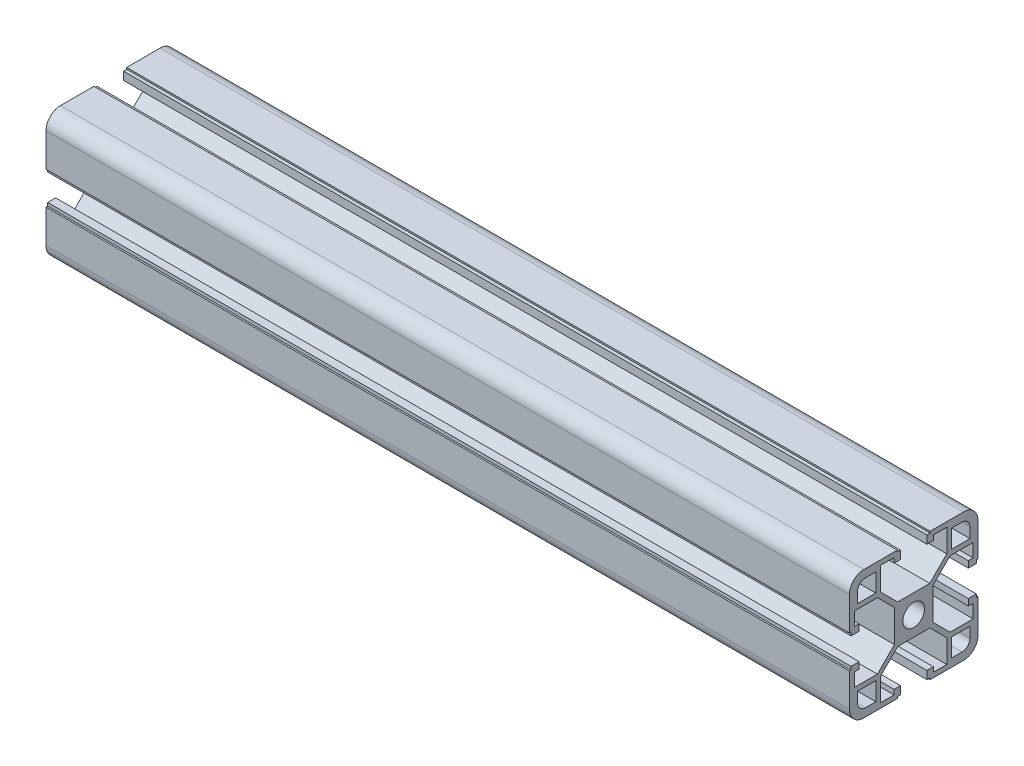
SolidWorks part; units mm, degrees
ref_plane "前视基准面" through (0, 0, 0) normal (0, 0, 1) x (1, 0, 0)
ref_plane "上视基准面" through (0, 0, 0) normal (0, 1, 0) x (1, 0, 0)
ref_plane "右视基准面" through (0, 0, 0) normal (1, 0, 0) x (0, 0, -1)
sketch "草图1" plane through (0, 0, 0) normal (0, 1, 0) x (1, 0, 0)
  line L0 (-142.4125, 0) -> (107.5875, 0)
  dimension "D1" = 250
other "铝型材 40 X 40L X R4.5(1)"
ref_plane "基准面1" through (-142.4125, 0, 0) normal (1, 0, 0) x (0, 0, -1)
sketch "Sketch1" plane through (-142.4125, 0, 0) normal (1, 0, 0) x (0, 0, -1)
  line L0 (-5.1, 20) -> (-5.1, 19.5)
  line L1 (-5.1, 19.5) -> (-4.1, 19.5)
  line L2 (-4.1, 19.5) -> (-4.1, 17)
  line L3 (-6.1, 18.5) -> (-10.3, 18.5)
  line L4 (-15.5, -20) -> (-5.1, -20)
  line L5 (-20, -15.5) -> (-20, -5.1)
  line L6 (15.5, 20) -> (5.1, 20)
  line L7 (20, 15.5) -> (20, 5.1)
  line L8 (0, 14.8756) -> (0, 0) construction
  line L9 (0, 0) -> (14.1675, 0) construction
  line L10 (-10.3, 18.5) -> (-10.3, 11.3)
  line L11 (-10.3, 11.3) -> (-5, 6)
  line L12 (-5, 6) -> (5, 6)
  line L13 (10.3, 11.3) -> (5, 6)
  line L14 (10.3, 18.5) -> (10.3, 11.3)
  line L15 (6.1, 18.5) -> (10.3, 18.5)
  line L16 (4.1, 19.5) -> (4.1, 17)
  line L17 (5.1, 19.5) -> (4.1, 19.5)
  line L18 (5.1, 20) -> (5.1, 19.5)
  line L19 (-5.1, 20) -> (-15.5, 20)
  line L20 (20, 5.1) -> (19.5, 5.1)
  line L21 (11.8, 17.5) -> (15, 17.5)
  line L22 (11.8, 17.5) -> (11.8, 11.8)
  line L23 (11.8, 11.8) -> (17.5, 11.8)
  line L24 (17.5, 15) -> (17.5, 11.8)
  line L25 (19.5, 5.1) -> (19.5, 4.1)
  line L26 (19.5, 4.1) -> (17, 4.1)
  line L27 (17, 6.1) -> (17, 4.1)
  line L28 (18.5, 6.1) -> (17, 6.1)
  line L29 (18.5, 6.1) -> (18.5, 10.3)
  line L30 (18.5, 10.3) -> (11.3, 10.3)
  line L31 (11.3, 10.3) -> (6, 5)
  line L32 (6, 5) -> (6, -5)
  line L33 (11.3, -10.3) -> (6, -5)
  line L34 (18.5, -10.3) -> (11.3, -10.3)
  line L35 (18.5, -6.1) -> (18.5, -10.3)
  line L36 (18.5, -6.1) -> (17, -6.1)
  line L37 (17, -4.1) -> (17, -6.1)
  line L38 (19.5, -4.1) -> (17, -4.1)
  line L39 (19.5, -5.1) -> (19.5, -4.1)
  line L40 (20, -5.1) -> (19.5, -5.1)
  line L41 (5.1, -20) -> (5.1, -19.5)
  line L42 (5.1, -19.5) -> (4.1, -19.5)
  line L43 (4.1, -19.5) -> (4.1, -17)
  line L44 (6.1, -17) -> (4.1, -17)
  line L45 (6.1, -18.5) -> (6.1, -17)
  line L46 (6.1, -18.5) -> (10.3, -18.5)
  line L47 (10.3, -18.5) -> (10.3, -11.3)
  line L48 (10.3, -11.3) -> (5, -6)
  line L49 (5, -6) -> (-5, -6)
  line L50 (-10.3, -11.3) -> (-5, -6)
  line L51 (-10.3, -18.5) -> (-10.3, -11.3)
  line L52 (-6.1, -18.5) -> (-10.3, -18.5)
  line L53 (-6.1, -18.5) -> (-6.1, -17)
  line L54 (-4.1, -17) -> (-6.1, -17)
  line L55 (-4.1, -19.5) -> (-4.1, -17)
  line L56 (-5.1, -19.5) -> (-4.1, -19.5)
  line L57 (-5.1, -20) -> (-5.1, -19.5)
  line L58 (-20, -5.1) -> (-19.5, -5.1)
  line L59 (5.1, -20) -> (15.5, -20)
  line L60 (-20, 5.1) -> (-20, 15.5)
  line L61 (-19.5, -5.1) -> (-19.5, -4.1)
  line L62 (-6.1, 18.5) -> (-6.1, 17)
  line L63 (-6.1, 17) -> (-4.1, 17)
  line L64 (6.1, 18.5) -> (6.1, 17)
  line L65 (4.1, 17) -> (6.1, 17)
  line L66 (-19.5, -4.1) -> (-17, -4.1)
  line L67 (-15, 17.5) -> (-11.8, 17.5)
  line L68 (-17.5, 15) -> (-17.5, 11.8)
  line L69 (-17.5, 11.8) -> (-11.8, 11.8)
  line L70 (-11.8, 17.5) -> (-11.8, 11.8)
  line L71 (-17, -6.1) -> (-17, -4.1)
  line L72 (-18.5, -6.1) -> (-17, -6.1)
  line L73 (-18.5, -6.1) -> (-18.5, -10.3)
  line L74 (-18.5, -10.3) -> (-11.3, -10.3)
  line L75 (-11.3, -10.3) -> (-6, -5)
  line L76 (-6, -5) -> (-6, 5)
  line L77 (-11.3, 10.3) -> (-6, 5)
  line L78 (-18.5, 10.3) -> (-11.3, 10.3)
  line L79 (-18.5, 6.1) -> (-18.5, 10.3)
  line L80 (-18.5, 6.1) -> (-17, 6.1)
  line L81 (-17, 4.1) -> (-17, 6.1)
  line L82 (-19.5, 4.1) -> (-17, 4.1)
  line L83 (-19.5, 5.1) -> (-19.5, 4.1)
  line L84 (-20, 5.1) -> (-19.5, 5.1)
  line L85 (20, -5.1) -> (20, -15.5)
  line L87 (-17.5, -11.8) -> (-11.8, -11.8)
  line L88 (-17.5, -11.8) -> (-17.5, -15)
  line L89 (-15, -17.5) -> (-11.8, -17.5)
  line L90 (-11.8, -11.8) -> (-11.8, -17.5)
  line L91 (11.8, -11.8) -> (17.5, -11.8)
  line L92 (11.8, -11.8) -> (11.8, -17.5)
  line L93 (11.8, -17.5) -> (15, -17.5)
  line L94 (17.5, -11.8) -> (17.5, -15)
  circle A0 centre (0, 0) radius 3.4
  arc A1 (-20, 15.5) -> (-15.5, 20) centre (-15.5, 15.5) cw
  arc A2 (20, 15.5) -> (15.5, 20) centre (15.5, 15.5) ccw
  arc A3 (-15.5, -20) -> (-20, -15.5) centre (-15.5, -15.5) cw
  arc A4 (15.5, -20) -> (20, -15.5) centre (15.5, -15.5) ccw
  arc A5 (-15, 17.5) -> (-17.5, 15) centre (-15, 15) ccw
  arc A6 (17.5, 15) -> (15, 17.5) centre (15, 15) ccw
  arc A7 (17.5, -15) -> (15, -17.5) centre (15, -15) cw
  arc A8 (-17.5, -15) -> (-15, -17.5) centre (-15, -15) ccw
  point P2 (0, 10)
  point P4 (0, 0)
  point P5 (-20, -20)
  point P6 (20, -20)
  point P7 (20, 20)
  point P8 (-20, 20)
  point P36 (-20, 20)
  point P39 (20, 20)
  point P121 (0, 0)
  dimension "D1" = 20.6
  dimension "D2" = 40
  dimension "D3" = 8.2
  dimension "D4" = 10.2
  dimension "D5" = 14
  dimension "D6" = 6.8
  dimension "D7" = 4.5
  dimension "D8" = 45
  dimension "D12" = 2.5
  dimension "D13" = 5.7
  dimension "D14" = 1.5
  dimension "D18" = 2.5
  dimension "D19" = 2.5
  dimension "D15" = 2.5
  dimension "D9" = 0.5
  dimension "D10" = 1.5
  dimension "D11" = 10
  dimension "D16" = 3
  dimension "D17" = 2
  dimension "D20" = 1.5
  dimension "D21" = 2.5
